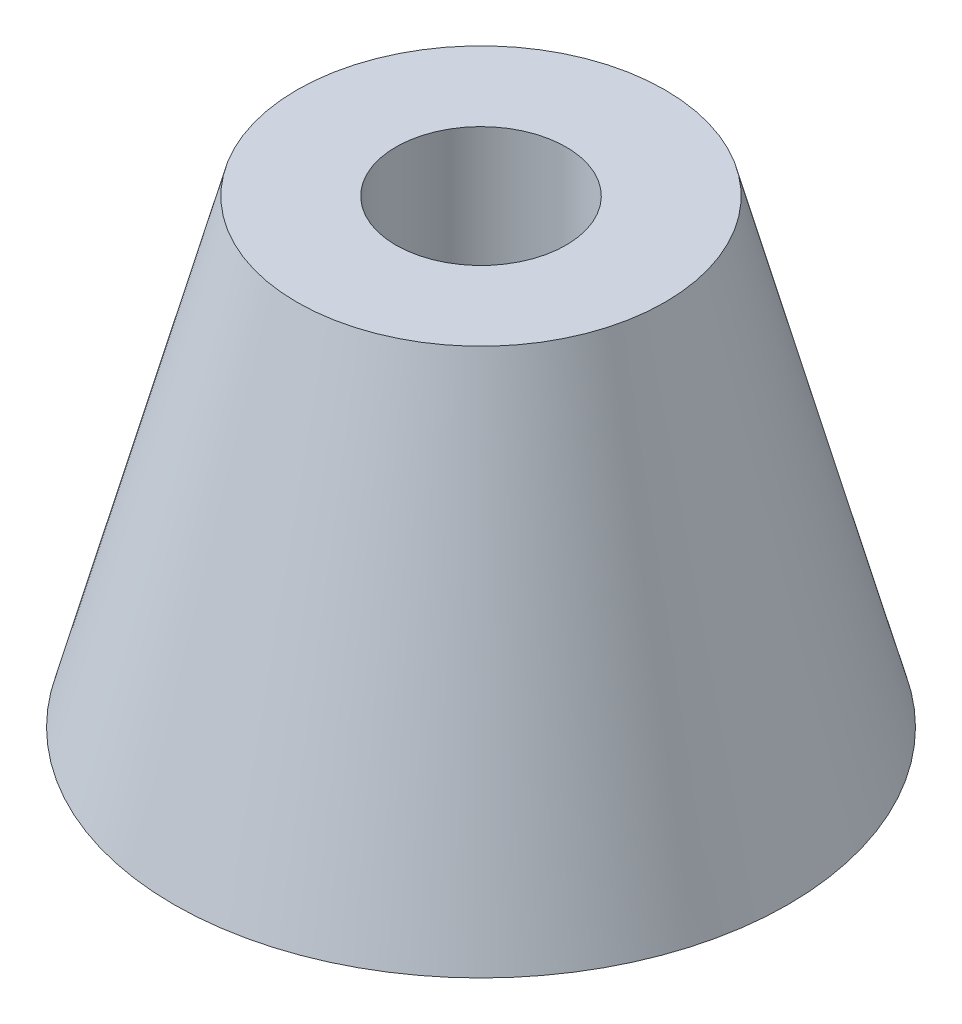
SolidWorks part; units mm, degrees
ref_plane "Front Plane" through (0, 0, 0) normal (0, 0, 1) x (1, 0, 0)
ref_plane "Top Plane" through (0, 0, 0) normal (0, 1, 0) x (1, 0, 0)
ref_plane "Right Plane" through (0, 0, 0) normal (1, 0, 0) x (0, 0, -1)
sketch "Sketch1" plane through (0, 0, 0) normal (0, 1, 0) x (1, 0, 0)
  circle A1 centre (0, 0) radius 4
  dimension "D2" = 8
extrude "Boss-Extrude1" add sketch "Sketch1" against normal blind 10 draft 15 draft outward yes
sketch "Sketch2" plane through (0, 0, 0) normal (0, 1, 0) x (1, 0, 0)
  circle A0 centre (0, 0) radius 1.85
  dimension "D1" = 3.7
extrude "Cut-Extrude1" cut sketch "Sketch2" against normal through all
